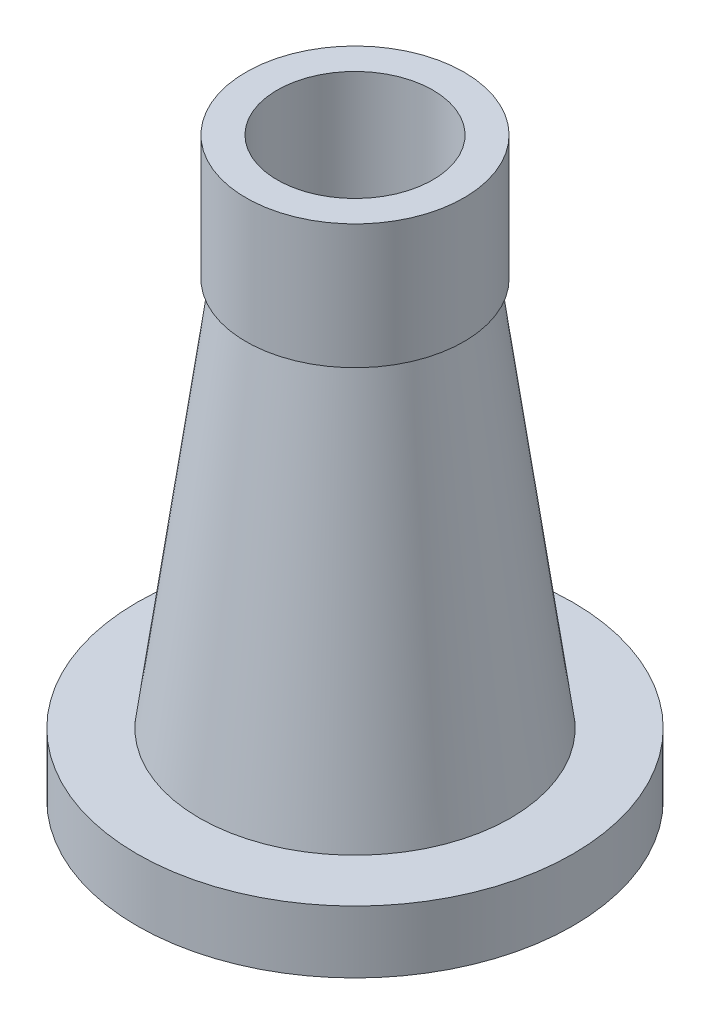
SolidWorks part; units mm, degrees
material "Gray Cast Iron"
ref_plane "Front Plane" through (0, 0, 0) normal (0, 0, 1) x (1, 0, 0)
ref_plane "Top Plane" through (0, 0, 0) normal (0, 1, 0) x (1, 0, 0)
ref_plane "Right Plane" through (0, 0, 0) normal (1, 0, 0) x (0, 0, -1)
sketch "Sketch1" plane through (0, 0, 0) normal (0, 0, 1) x (1, 0, 0)
  line L35 (0, 0) -> (0, 205.3424) construction
  line L36 (70, 0) -> (70, 20)
  line L37 (70, 20) -> (50, 20)
  line L38 (50, 20) -> (33, 145)
  line L39 (33, 145) -> (35, 145)
  line L40 (35, 145) -> (35, 185)
  line L41 (35, 185) -> (25, 185)
  line L42 (25, 185) -> (25, 129.6172)
  line L43 (25, 129.6172) -> (42.2199, 3)
  line L44 (42.2199, 3) -> (50, 3)
  line L45 (50, 3) -> (50, 0)
  line L46 (50, 0) -> (70, 0)
  dimension "D1" = 20
  dimension "D2" = 70
  dimension "D3" = 50
  dimension "D4" = 3
  dimension "D5" = 40
  dimension "D6" = 35
  dimension "D7" = 25
  dimension "D8" = 33
  dimension "D9" = 10
  dimension "D10" = 185
revolve "Revolve1" add sketch "Sketch1" angle 360 about L35
